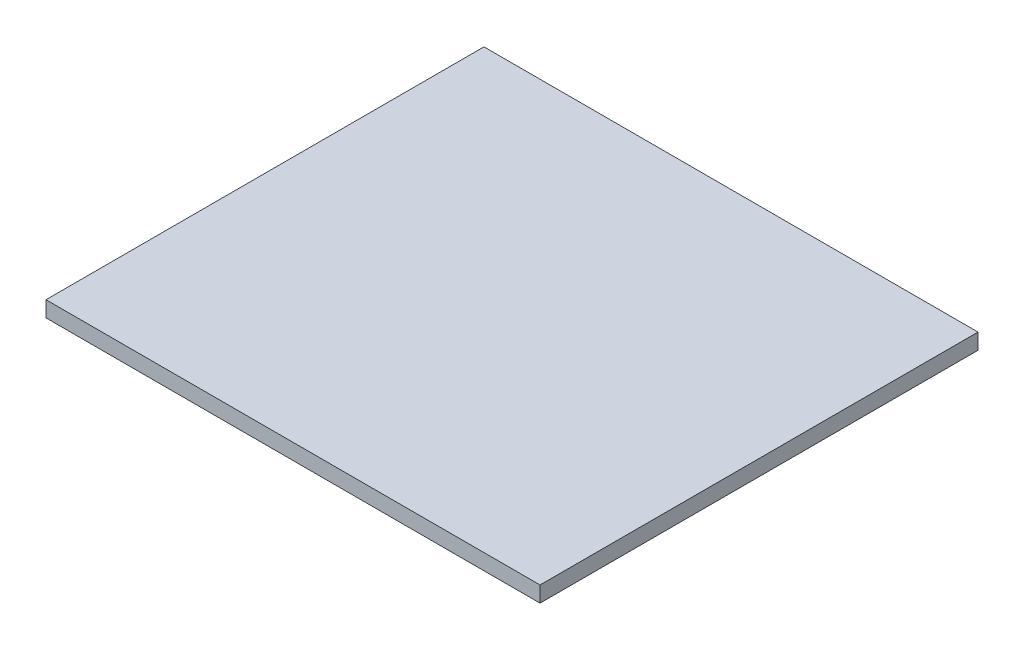
SolidWorks part; units mm, degrees
ref_plane "Спереди" through (0, 0, 0) normal (0, 0, 1) x (1, 0, 0)
ref_plane "Сверху" through (0, 0, 0) normal (0, 1, 0) x (1, 0, 0)
ref_plane "Справа" through (0, 0, 0) normal (1, 0, 0) x (0, 0, -1)
sketch "Эскиз1" plane through (0, 0, 0) normal (0, 1, 0) x (1, 0, 0)
  line L1 (282, 250) -> (-282, 250)
  line L2 (282, 250) -> (282, -250)
  line L3 (282, -250) -> (-282, -250)
  line L4 (-282, 250) -> (-282, -250)
  line L5 (282, 250) -> (-282, -250) construction
  line L6 (282, -250) -> (-282, 250) construction
  point P0 (0, 0)
  dimension "D1" = 564
  dimension "D2" = 500
extrude "Бобышка-Вытянуть1" add sketch "Эскиз1" along normal blind 18
